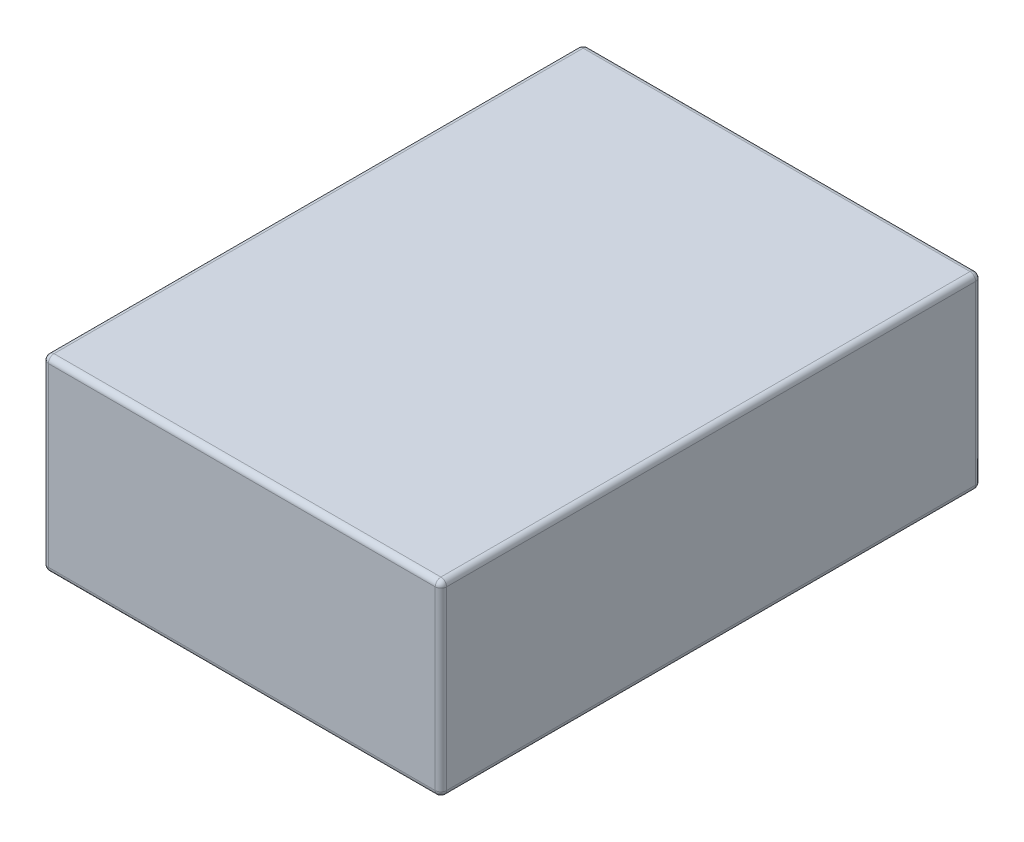
SolidWorks part; units mm, degrees
ref_plane "Front Plane" through (0, 0, 0) normal (0, 0, 1) x (1, 0, 0)
ref_plane "Top Plane" through (0, 0, 0) normal (0, 1, 0) x (1, 0, 0)
ref_plane "Right Plane" through (0, 0, 0) normal (1, 0, 0) x (0, 0, -1)
sketch "Sketch1" plane through (0, 0, 0) normal (0, 1, 0) x (1, 0, 0)
  line L1 (0, 0) -> (70, 0)
  line L2 (0, 0) -> (0, 95)
  line L3 (0, 95) -> (70, 95)
  line L4 (70, 0) -> (70, 95)
  dimension "D1" = 95
  dimension "D2" = 70
extrude "Boss-Extrude1" add sketch "Sketch1" along normal blind 33
fillet "Fillet1" radius 1 12 edges at (0, 16.5, 0) (70, 16.5, 0) (70, 16.5, -95) (0, 16.5, -95) (35, 33, -95) (70, 33, -47.5) (35, 33, 0) (0, 33, -47.5) (35, 0, 0) (70, 0, -47.5) (35, 0, -95) (0, 0, -47.5)
sketch "Sketch5" plane through (0, 33, 0) normal (0, 1, 0) x (1, 0, 0)
  line L0 (1, 94) -> (69, 1) construction
  text T0 "nikhon charger MH-25A" font "Arial Narrow" height in points 28
extrude "Boss-Extrude2" add sketch "Sketch5" against normal offset from surface (2 mm away) 2 up to face at (35, 33, -47.5)
